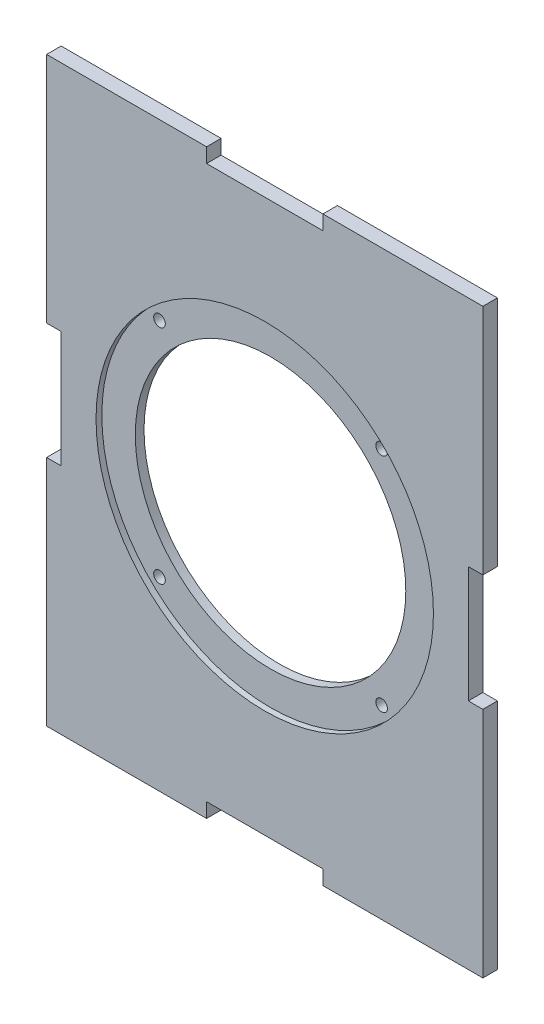
SolidWorks part; units mm, degrees
ref_plane "Alzado" through (0, 0, 0) normal (0, 0, 1) x (1, 0, 0)
ref_plane "Planta" through (0, 0, 0) normal (0, 1, 0) x (1, 0, 0)
ref_plane "Vista lateral" through (0, 0, 0) normal (1, 0, 0) x (0, 0, -1)
sketch "Croquis1" plane through (0, 0, 0) normal (0, 0, 1) x (1, 0, 0)
  line L0 (0, 0) -> (-38.1838, 38.1838) construction
  line L1 (-75, -100) -> (75, -100)
  line L2 (-75, -100) -> (-75, 100)
  line L3 (-75, 100) -> (75, 100)
  line L4 (75, -100) -> (75, 100)
  line L5 (-75, -100) -> (75, 100) construction
  line L6 (-75, 100) -> (75, -100) construction
  circle A0 centre (0, 0) radius 46.5
  circle A1 centre (0, 0) radius 54 construction
  circle A2 centre (-38.1838, 38.1838) radius 2
  circle A3 centre (38.1838, 38.1838) radius 2
  circle A4 centre (38.1838, -38.1838) radius 2
  circle A5 centre (-38.1838, -38.1838) radius 2
  point P0 (0, 0)
  point P20 (0, 0)
  dimension "D3" = 93
  dimension "D4" = 108
  dimension "D6" = 4
  dimension "D1" = 150
  dimension "D2" = 200
  dimension "D5" = 45
  dimension "D7" = 4
extrude "Saliente-Extruir1" add sketch "Croquis1" along normal blind 5
sketch "Croquis2" plane through (0, 0, 5) normal (0, 0, 1) x (1, 0, 0)
  circle A0 centre (0, 0) radius 58
  dimension "D1" = 116
extrude "Cortar-Extruir1" cut sketch "Croquis2" against normal blind 2
sketch "Croquis3" plane through (0, 0, 5) normal (0, 0, 1) x (1, 0, 0)
  line L0 (75, 100) -> (-75, 100) construction
  line L1 (20, 100) -> (-20, 100)
  line L2 (20, 100) -> (20, 95)
  line L3 (20, 95) -> (-20, 95)
  line L4 (-20, 100) -> (-20, 95)
  line L5 (-75, 0) -> (75, 0) construction
  line L6 (-75, 100) -> (-75, -100) construction
  line L7 (75, -100) -> (75, 100) construction
  line L8 (-20, -100) -> (-20, -95)
  line L9 (20, -95) -> (-20, -95)
  line L10 (20, -100) -> (20, -95)
  line L11 (20, -100) -> (-20, -100)
  line L12 (0, 0) -> (0, 37.5115) construction
  line L13 (-75, -20) -> (-70, -20)
  line L14 (-75, -20) -> (-75, 20)
  line L15 (-75, 20) -> (-70, 20)
  line L16 (-70, -20) -> (-70, 20)
  line L17 (70, -20) -> (70, 20)
  line L18 (75, 20) -> (70, 20)
  line L19 (75, -20) -> (75, 20)
  line L20 (75, -20) -> (70, -20)
  point P6 (0, 100)
  point P7 (0, 100)
  point P23 (-75, 0)
  dimension "D1" = 40
  dimension "D2" = 5
  dimension "D3" = 5
  dimension "D4" = 40
extrude "Cortar-Extruir2" cut sketch "Croquis3" against normal up to vertex
